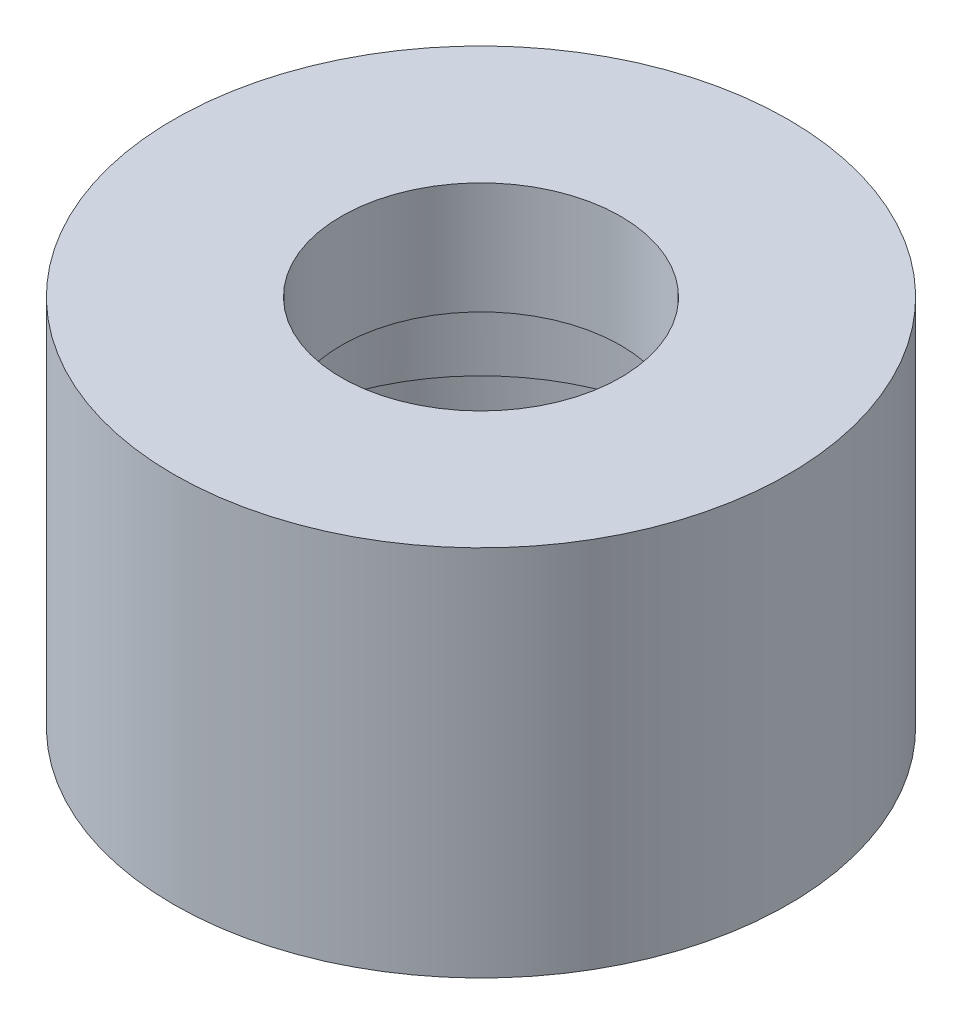
SolidWorks part; units mm, degrees
ref_plane "Front Plane" through (0, 0, 0) normal (0, 0, 1) x (1, 0, 0)
ref_plane "Top Plane" through (0, 0, 0) normal (0, 1, 0) x (1, 0, 0)
ref_plane "Right Plane" through (0, 0, 0) normal (1, 0, 0) x (0, 0, -1)
sketch "Sketch1" plane through (0, 0, 0) normal (0, 1, 0) x (1, 0, 0)
  circle A0 centre (0, 0) radius 16.5
  dimension "D1" = 33
extrude "Boss-Extrude1" add sketch "Sketch1" along normal blind 20
ref_plane "Plane1" through (0, 0, 16.5) normal (0, 0, 1) x (1, 0, 0)
sketch "Sketch2" plane through (0, 0, 16.5) normal (0, 0, 1) x (1, 0, 0)
  line L0 (-16.5, 0) -> (16.5, 0) construction
  circle A0 centre (0, 14) radius 2
  dimension "D1" = 4
  dimension "D2" = 14
sketch "Sketch3" plane through (0, 0, 0) normal (0, -1, 0) x (1, 0, 0)
  circle A0 centre (0, 0) radius 7.5
  dimension "D1" = 15
extrude "Cut-Extrude2" cut sketch "Sketch3" against normal through all
sketch "Sketch7" plane through (0, 0, 0) normal (0, -1, 0) x (1, 0, 0)
  circle A1 centre (0, 0) radius 11.5
  circle A2 centre (0, 0) radius 7.5
  dimension "D1" = 15
  dimension "D2" = 23
extrude "Cut-Extrude3" cut sketch "Sketch7" against normal blind 14
ref_plane "Plane4" through (0, 0, 0) normal (1, 0, 0) x (0, 0, -1)
sketch "Sketch12" plane through (0, 0, 0) normal (1, 0, 0) x (0, 0, -1)
  line L0 (-8, -0.4461) -> (-8, 8.2)
  line L1 (-8, 8.2) -> (8, 8.2)
  line L2 (8, 8.2) -> (8, 4.1)
  line L3 (8, 4.1) -> (-3.5, 4.1)
  line L4 (-3.5, 4.1) -> (-3.5, -0.4461)
  line L5 (-3.5, -0.4461) -> (-8, -0.4461)
  line L6 (0, 0) -> (0, 8.2) construction
  dimension "D1" = 16
  dimension "D2" = 4.5
  dimension "D3" = 8
  dimension "D4" = 4.1
  dimension "D5" = 4.1
extrude "Cut-Extrude4" cut sketch "Sketch12" along normal offset from surface (12.9545 mm away) 2
pattern_circular "CirPattern1" count 3 over 360 about axis through (0, 0, 0) along (0, 1, 0) of "Cut-Extrude4"
